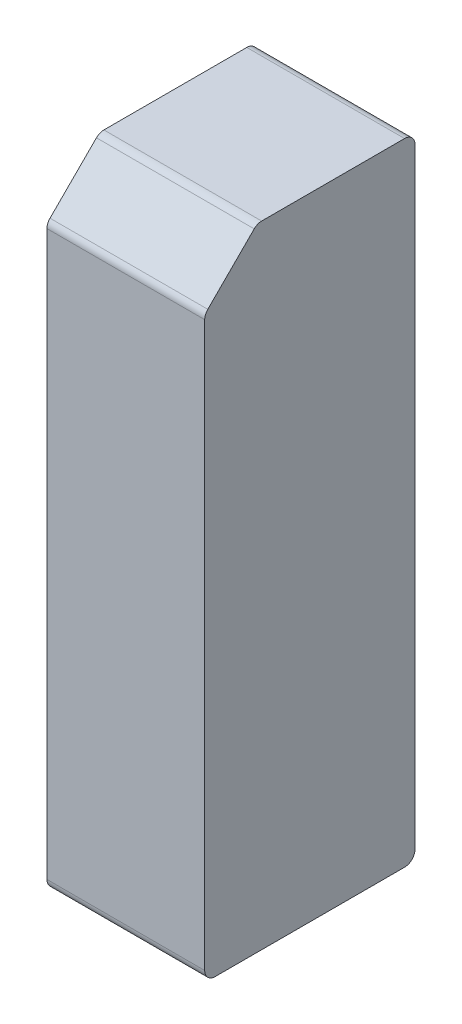
SolidWorks part; units mm, degrees
material "PE High Density"
ref_plane "Front Plane" through (0, 0, 0) normal (0, 0, 1) x (1, 0, 0)
ref_plane "Top Plane" through (0, 0, 0) normal (0, 1, 0) x (1, 0, 0)
ref_plane "Right Plane" through (0, 0, 0) normal (1, 0, 0) x (0, 0, -1)
other "Bounding Box"
ref_plane "Default Plane" through (13.8565, 3.175, 6.7999) normal (0, -1, 0) x (-1, 0, 0)
sketch "Sketch1" plane through (0, 0, 0) normal (1, 0, 0) x (0, 0, -1)
  line L0 (-6.35, 17.4625) -> (-3.175, 20.6375)
  line L1 (-6.35, -17.4625) -> (6.35, -17.4625)
  line L2 (-6.35, -17.4625) -> (-6.35, 17.4625)
  line L3 (-6.35, 17.4625) -> (6.35, 17.4625) construction
  line L4 (6.35, -17.4625) -> (6.35, 17.4625)
  line L5 (-6.35, -17.4625) -> (6.35, 17.4625) construction
  line L6 (-6.35, 17.4625) -> (6.35, -17.4625) construction
  line L7 (-3.175, 20.6375) -> (6.35, 20.6375)
  line L8 (6.35, 20.6375) -> (6.35, 17.4625)
  point P0 (0, 0)
  point P6 (6.35, 7.443)
  point P9 (6.35, 25.6294)
  point P10 (-6.35, 15.9816)
  point P11 (6.35, 13.9504)
  point P12 (3.0849, 25.4)
  point P13 (-6.35, 15.5809)
  point P14 (6.35, 21.9219)
  dimension "D1" = 12.7
  dimension "D2" = 3.175
  dimension "D3" = 38.1
  dimension "D4" = 45
extrude "Boss-Extrude1" add sketch "Sketch1" along normal blind 9.525
fillet "Fillet1" radius 0.635 5 edges at (4.7625, -17.4625, 6.35) (4.7625, -17.4625, -6.35) (4.7625, 20.6375, -6.35) (4.7625, 20.6375, 3.175) (4.7625, 17.4625, 6.35)
